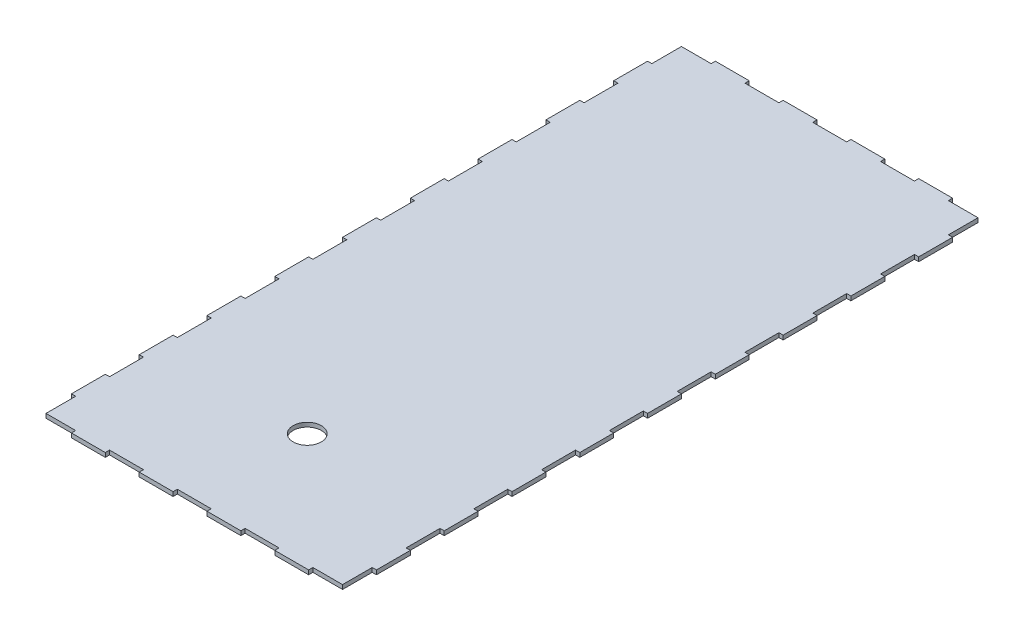
SolidWorks part; units mm, degrees
ref_plane "Front Plane" through (0, 0, 0) normal (0, 0, 1) x (1, 0, 0)
ref_plane "Top Plane" through (0, 0, 0) normal (0, 1, 0) x (1, 0, 0)
ref_plane "Right Plane" through (0, 0, 0) normal (1, 0, 0) x (0, 0, -1)
sketch "Sketch1" plane through (0, 0, 0) normal (0, 1, 0) x (1, 0, 0)
  line L1 (-105, -225) -> (105, -225)
  line L2 (-105, -225) -> (-105, 225)
  line L3 (-105, 225) -> (105, 225)
  line L4 (105, -225) -> (105, 225)
  line L5 (-105, -225) -> (105, 225) construction
  line L6 (-105, 225) -> (105, -225) construction
  circle A0 centre (0, -145) radius 10
  point P0 (0, 0)
  dimension "D3" = 20
  dimension "D4" = 105
  dimension "D5" = 80
  dimension "D1" = 210
  dimension "D2" = 450
extrude "Boss-Extrude1" add sketch "Sketch1" along normal blind 3
sketch "Sketch2" plane through (0, 3, 0) normal (0, 1, 0) x (1, 0, 0)
  line L0 (105, 225) -> (-105, 225) construction
  line L1 (-84, 225) -> (-60, 225)
  line L2 (-84, 225) -> (-84, 228)
  line L3 (-84, 228) -> (-60, 228)
  line L4 (-60, 225) -> (-60, 228)
  line L5 (-36, 225) -> (-36, 228)
  line L6 (-36, 225) -> (-12, 225)
  line L7 (-12, 225) -> (-12, 228)
  line L8 (-36, 228) -> (-12, 228)
  line L9 (12, 225) -> (12, 228)
  line L10 (12, 225) -> (36, 225)
  line L11 (36, 225) -> (36, 228)
  line L12 (12, 228) -> (36, 228)
  line L13 (60, 225) -> (60, 228)
  line L14 (60, 225) -> (84, 225)
  line L15 (84, 225) -> (84, 228)
  line L16 (60, 228) -> (84, 228)
  line L17 (-36, -228) -> (-36, -225)
  line L18 (-36, -228) -> (-12, -228)
  line L19 (-12, -228) -> (-12, -225)
  line L20 (-36, -225) -> (-12, -225)
  line L21 (12, -228) -> (12, -225)
  line L22 (12, -228) -> (36, -228)
  line L23 (36, -228) -> (36, -225)
  line L24 (12, -225) -> (36, -225)
  line L25 (60, -228) -> (60, -225)
  line L26 (60, -228) -> (84, -228)
  line L27 (84, -228) -> (84, -225)
  line L28 (60, -225) -> (84, -225)
  line L29 (-84, -228) -> (-84, -225)
  line L30 (-84, -228) -> (-60, -228)
  line L31 (-60, -228) -> (-60, -225)
  line L32 (-84, -225) -> (-60, -225)
  line L33 (-84, 225) -> (-84, -228) construction
  line L34 (-12, 225) -> (12, 225)
  line L35 (-12, -225) -> (12, -225)
  line L38 (105, -225) -> (105, 225) construction
  point P6 (0, 225)
  point P7 (-72, 225)
  point P8 (0, -225)
  dimension "D1" = 3
  dimension "D2" = 24
  dimension "D5" = 453
  dimension "D6" = 24
  dimension "D7" = 450
  dimension "D3" = 4
  dimension "D4" = 2
sketch "Sketch3" plane through (0, 3, 0) normal (0, 1, 0) x (1, 0, 0)
  line L0 (-105, 225) -> (-105, -225) construction
  line L1 (-105, 204) -> (-108, 204)
  line L2 (-105, 204) -> (-105, 180)
  line L3 (-105, 180) -> (-108, 180)
  line L4 (-108, 204) -> (-108, 180)
  line L5 (108, 204) -> (108, 180)
  line L6 (108, 204) -> (105, 204)
  line L7 (105, 204) -> (105, 180)
  line L8 (108, 180) -> (105, 180)
  line L9 (108, 156) -> (108, 132)
  line L10 (108, 156) -> (105, 156)
  line L11 (105, 156) -> (105, 132)
  line L12 (108, 132) -> (105, 132)
  line L13 (108, 108) -> (108, 84)
  line L14 (108, 108) -> (105, 108)
  line L15 (105, 108) -> (105, 84)
  line L16 (108, 84) -> (105, 84)
  line L17 (108, 60) -> (108, 36)
  line L18 (108, 60) -> (105, 60)
  line L19 (105, 60) -> (105, 36)
  line L20 (108, 36) -> (105, 36)
  line L21 (108, 12) -> (108, -12)
  line L22 (108, 12) -> (105, 12)
  line L23 (105, 12) -> (105, -12)
  line L24 (108, -12) -> (105, -12)
  line L25 (108, -36) -> (108, -60)
  line L26 (108, -36) -> (105, -36)
  line L27 (105, -36) -> (105, -60)
  line L28 (108, -60) -> (105, -60)
  line L29 (108, -84) -> (108, -108)
  line L30 (108, -84) -> (105, -84)
  line L31 (105, -84) -> (105, -108)
  line L32 (108, -108) -> (105, -108)
  line L33 (108, -132) -> (108, -156)
  line L34 (108, -132) -> (105, -132)
  line L35 (105, -132) -> (105, -156)
  line L36 (108, -156) -> (105, -156)
  line L37 (108, -180) -> (108, -204)
  line L38 (108, -180) -> (105, -180)
  line L39 (105, -180) -> (105, -204)
  line L40 (108, -204) -> (105, -204)
  line L41 (-105, 156) -> (-105, 132)
  line L42 (-105, 156) -> (-108, 156)
  line L43 (-108, 156) -> (-108, 132)
  line L44 (-105, 132) -> (-108, 132)
  line L45 (-105, 108) -> (-105, 84)
  line L46 (-105, 108) -> (-108, 108)
  line L47 (-108, 108) -> (-108, 84)
  line L48 (-105, 84) -> (-108, 84)
  line L49 (-105, 60) -> (-105, 36)
  line L50 (-105, 60) -> (-108, 60)
  line L51 (-108, 60) -> (-108, 36)
  line L52 (-105, 36) -> (-108, 36)
  line L53 (-105, 12) -> (-105, -12)
  line L54 (-105, 12) -> (-108, 12)
  line L55 (-108, 12) -> (-108, -12)
  line L56 (-105, -12) -> (-108, -12)
  line L57 (-105, -36) -> (-105, -60)
  line L58 (-105, -36) -> (-108, -36)
  line L59 (-108, -36) -> (-108, -60)
  line L60 (-105, -60) -> (-108, -60)
  line L61 (-105, -84) -> (-105, -108)
  line L62 (-105, -84) -> (-108, -84)
  line L63 (-108, -84) -> (-108, -108)
  line L64 (-105, -108) -> (-108, -108)
  line L65 (-105, -132) -> (-105, -156)
  line L66 (-105, -132) -> (-108, -132)
  line L67 (-108, -132) -> (-108, -156)
  line L68 (-105, -156) -> (-108, -156)
  line L69 (-105, -180) -> (-105, -204)
  line L70 (-105, -180) -> (-108, -180)
  line L71 (-108, -180) -> (-108, -204)
  line L72 (-105, -204) -> (-108, -204)
  line L73 (-105, 204) -> (108, 204) construction
  line L74 (-105, 204) -> (-105, 156) construction
  point P7 (-105, 0)
  dimension "D1" = 3
  dimension "D2" = 24
  dimension "D5" = 213
  dimension "D6" = 48
  dimension "D3" = 2
  dimension "D4" = 9
extrude "Boss-Extrude3" add sketch "Sketch3" against normal blind 3
extrude "Boss-Extrude4" add sketch "Sketch2" against normal blind 3 contours L1 L4 L3 L2 | L8 L5 L6 L7 | L12 L9 L10 L11 | L16 L13 L14 L15 | L32 L29 L30 L31 | L20 L17 L18 L19 | L24 L21 L22 L23 | L28 L27 L26 L25
